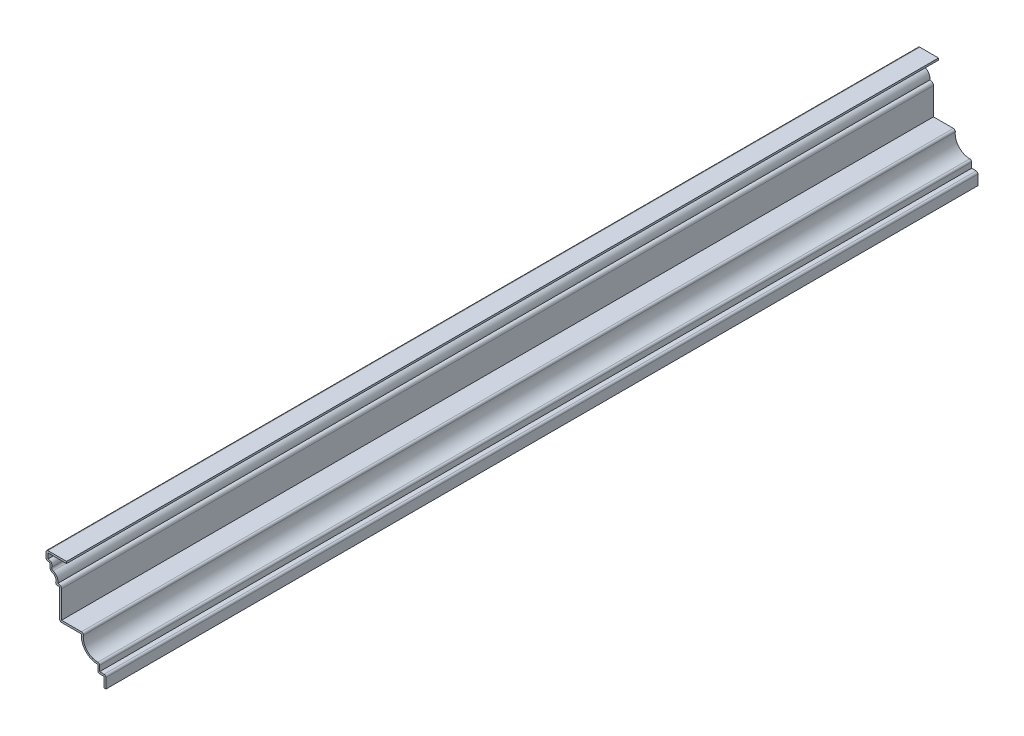
SolidWorks part; units mm, degrees
ref_plane "Front Plane" through (0, 0, 0) normal (0, 0, 1) x (1, 0, 0)
ref_plane "Top Plane" through (0, 0, 0) normal (0, 1, 0) x (1, 0, 0)
ref_plane "Right Plane" through (0, 0, 0) normal (1, 0, 0) x (0, 0, -1)
sketch "Sketch1" plane through (0, 0, 0) normal (0, 0, 1) x (1, 0, 0)
  line L8 (136.6015, 371) -> (721.2681, 371) construction
  line L9 (0, 0) -> (0, 64.7026) construction
  line L10 (-50.8, 79.375) -> (-32.8237, 79.375)
  line L11 (-50.8, 71.4375) -> (-50.8, 79.375)
  line L12 (-48.8156, 71.4375) -> (-50.8, 71.4375)
  line L13 (-38.8937, 30.9562) -> (-38.8937, 56.3562)
  line L14 (-19.8437, 30.9562) -> (-38.8937, 30.9562)
  line L15 (-5.5562, 8.7312) -> (-5.5562, 15.0812)
  line L16 (0, 8.7312) -> (-5.5562, 8.7312)
  line L17 (0, 0) -> (0, 8.7312)
  arc A6 (-47.2309, 69.1412) -> (-48.8156, 71.4375) centre (-48.8156, 69.7425) ccw
  arc A7 (-45.1521, 64.7026) -> (-47.2309, 69.1412) centre (-44.0392, 67.93) cw
  arc A8 (-42.226, 58.8456) -> (-45.1521, 64.7026) centre (-46.6767, 60.2815) ccw
  arc A9 (-40.2538, 57.1808) -> (-42.226, 58.8456) centre (-40.8987, 58.4174) cw
  arc A10 (-38.8937, 56.3562) -> (-40.2538, 57.1808) centre (-39.8238, 56.3562) ccw
  arc A11 (-5.5562, 15.0812) -> (-19.8437, 30.9562) centre (-5.5562, 29.4481) cw
  dimension "D12" = 42.226
  dimension "D1" = 1.695
  dimension "D2" = 3.4138
  dimension "D3" = 4.6766
  dimension "D4" = 1.3946
  dimension "D5" = 0.93
  dimension "D6" = 14.3669
  dimension "D7" = 5.5562
  dimension "D8" = 19.8437
  dimension "D9" = 32.8237
  dimension "D10" = 38.8937
  dimension "D11" = 40.2538
  dimension "D13" = 44.0392
  dimension "D14" = 47.2309
  dimension "D15" = 8.7312
  dimension "D16" = 15.0812
  dimension "D17" = 56.3562
  dimension "D20" = 50.8
  dimension "D30" = 79.375
  dimension "D31" = 371
extrude "Extrude-Thin1" add sketch "Sketch1" against normal blind 762 thin contours L17 L16 L15 A11 L14 L13 A10 A9 A8 A7 A6 L12 L11 L10
fillet "Fillet1" radius 1.651 7 edges at (1.651, 10.3822, -381) (-5.5562, 8.7312, -381) (-3.9052, 16.8399, -381) (-17.8734, 32.6073, -381) (-38.8937, 30.9562, -381) (-50.8, 71.4375, -381) (-50.8, 79.375, -381)
